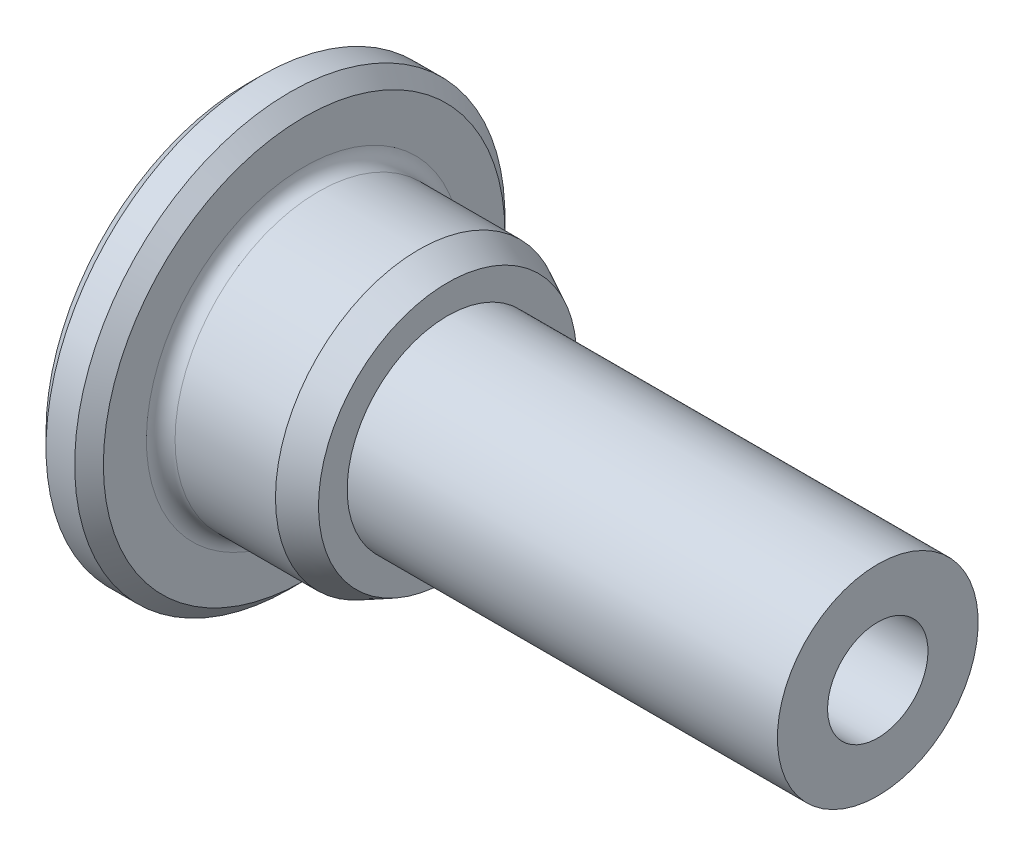
SolidWorks part; units mm, degrees
material "Alloy Steel (SS)"
ref_plane "Front Plane" through (0, 0, 0) normal (0, 0, 1) x (1, 0, 0)
ref_plane "Top Plane" through (0, 0, 0) normal (0, 1, 0) x (1, 0, 0)
ref_plane "Right Plane" through (0, 0, 0) normal (1, 0, 0) x (0, 0, -1)
sketch "Sketch1" plane through (0, 0, 0) normal (0, 0, 1) x (1, 0, 0)
  line L0 (0, 0) -> (0, 7.5)
  line L1 (0, 7.5) -> (2, 7.5)
  line L2 (2, 7.5) -> (2, 5)
  line L3 (2, 5) -> (6, 5)
  line L4 (6, 5) -> (7, 4.5)
  line L5 (7, 3.5) -> (22, 3.5)
  line L6 (22, 3.5) -> (22, 0)
  line L7 (22, 0) -> (0, 0)
  line L8 (0, 0) -> (25.3786, 0) construction
  line L9 (7, 4.5) -> (7, 3.5)
  dimension "D1" = 7.5
  dimension "D2" = 5
  dimension "D3" = 1
  dimension "D4" = 3.5
  dimension "D5" = 2
  dimension "D6" = 4
  dimension "D7" = 1
  dimension "D8" = 15
revolve "Revolve1" add sketch "Sketch1" angle 360 about L8
fillet "Fillet1" radius 0.5 1 edges at (2, -5, 0)
chamfer "Chamfer1" distance 0.5 angle 45 2 edges at (0, -7.5, 0) (2, -7.5, 0)
sketch "Sketch2" plane through (22, 0, 0) normal (1, 0, 0) x (0, 0, -1)
  circle A0 centre (0, 0) radius 1.75
  dimension "D1" = 3.5
extrude "Cut-Extrude1" cut sketch "Sketch2" against normal through all
chamfer "Chamfer2" distance 1 angle 45 1 edges at (0, 1.75, 0)
